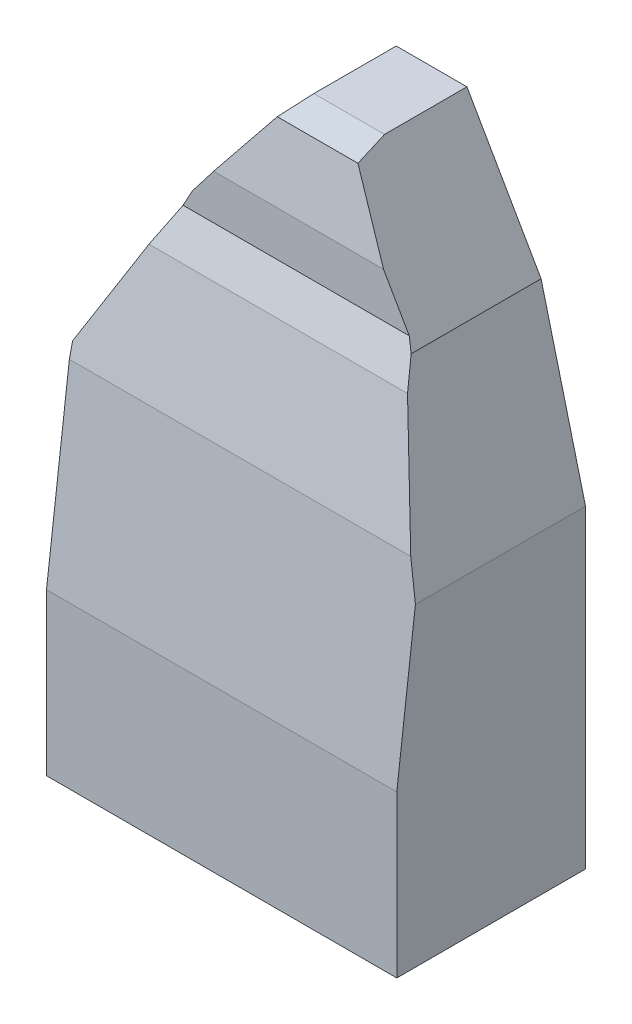
SolidWorks part; units mm, degrees
ref_plane "Front Plane" through (0, 0, 0) normal (0, 0, 1) x (1, 0, 0)
ref_plane "Top Plane" through (0, 0, 0) normal (0, 1, 0) x (1, 0, 0)
ref_plane "Right Plane" through (0, 0, 0) normal (1, 0, 0) x (0, 0, -1)
sketch "Sketch1" plane through (0, 0, 0) normal (0, 0, 1) x (1, 0, 0)
  line L0 (0, 0) -> (431.8, 0)
  line L1 (431.8, 0) -> (431.8, 387.4034)
  line L2 (431.8, 387.4034) -> (377.0655, 602.775)
  line L3 (377.0655, 602.775) -> (285.6418, 762)
  line L4 (285.6418, 762) -> (198.5042, 762)
  line L5 (198.5042, 762) -> (102.4538, 637.1345)
  line L6 (102.4538, 637.1345) -> (0, 448.2353)
  line L7 (0, 448.2353) -> (0, 0)
  dimension "D1" = 762
  dimension "D2" = 431.8
extrude "Boss-Extrude1" add sketch "Sketch1" along normal blind 101.6
sketch "Sketch2" plane through (0, 0, 0) normal (-1, 0, 0) x (0, 0, 1)
  line L0 (101.6, 0) -> (232.6217, 0)
  line L1 (232.6217, 0) -> (232.6217, 198.6482)
  line L2 (232.6217, 198.6482) -> (204.4518, 430.5066)
  line L3 (204.4518, 430.5066) -> (172.7805, 570.8119)
  line L4 (172.7805, 570.8119) -> (155.0893, 615.7047)
  line L5 (155.0893, 615.7047) -> (155.0893, 670.9083)
  line L6 (155.0893, 670.9083) -> (139.6079, 752.7874)
  line L8 (139.6079, 752.7874) -> (101.6, 762)
  line L9 (101.6, 762) -> (101.6, 0)
  dimension "D1" = 0
  dimension "D2" = 0
extrude "Boss-Extrude2" add sketch "Sketch2" against normal up to surface (431.8 mm away) up to face at (431.8, 193.7017, 50.8)
sketch "Sketch3" plane through (0, 0, 101.6) normal (0, 0, -1) x (-1, 0, 0)
  line L0 (0, 448.2353) -> (-102.0796, 636.4445)
  line L1 (0, 448.2353) -> (-102.4538, 637.1345) construction
  line L2 (-102.0796, 636.4445) -> (-205.0523, 770.5126)
  line L3 (-102.4538, 637.1345) -> (-198.5042, 762) construction
  line L4 (-205.0523, 770.5126) -> (-205.0523, 987.3428)
  line L5 (-205.0523, 987.3428) -> (227.8795, 941.9217)
  line L6 (227.8795, 941.9217) -> (179.7159, 482.8494)
  line L7 (179.7159, 482.8494) -> (0, 448.2353)
extrude "Cut-Extrude1" cut sketch "Sketch3" against normal through all
sketch "Sketch4" plane through (0, 0, 101.6) normal (0, 0, -1) x (-1, 0, 0)
  line L0 (-431.8, 387.4034) -> (-377.0655, 602.775)
  line L1 (-377.0655, 602.775) -> (-285.6418, 762)
  line L2 (-285.6418, 762) -> (-386.6478, 961.5261)
  line L3 (-386.6478, 961.5261) -> (-935.091, 961.5261)
  line L4 (-935.091, 961.5261) -> (-884.9139, 472.9491)
  line L5 (-884.9139, 472.9491) -> (-431.8, 387.4034)
extrude "Cut-Extrude2" cut sketch "Sketch4" against normal through all
